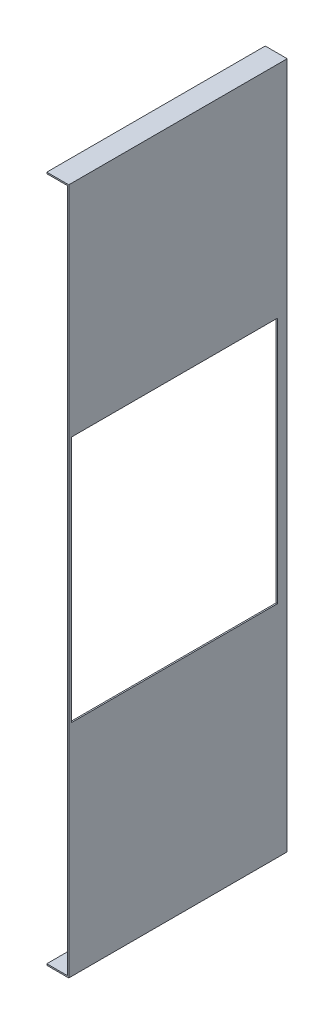
SolidWorks part; units mm, degrees
material "1023 Carbon Steel Sheet (SS)"
ref_plane "Front Plane" through (0, 0, 0) normal (0, 0, 1) x (1, 0, 0)
ref_plane "Top Plane" through (0, 0, 0) normal (0, 1, 0) x (1, 0, 0)
ref_plane "Right Plane" through (0, 0, 0) normal (1, 0, 0) x (0, 0, -1)
sketch "Sketch1" plane through (0, 0, 0) normal (0, 0, 1) x (1, 0, 0)
  line L0 (-0.5, -249) -> (-15.5, -249)
  line L2 (-0.5, 249) -> (-0.5, -249)
  line L4 (0.5, 249) -> (0.5, -249)
  line L5 (-0.5, 249) -> (0.5, -249) construction
  line L6 (-0.5, -249) -> (0.5, 249) construction
  line L7 (0.5, -250) -> (-15.5, -250)
  line L8 (0.5, -249) -> (0.5, -250)
  line L9 (-15.5, -249) -> (-15.5, -250)
  line L10 (0, 0) -> (-2.3545, 0) construction
  line L11 (0.5, 249) -> (0.5, 250)
  line L12 (-15.5, 249) -> (-15.5, 250)
  line L13 (0.5, 250) -> (-15.5, 250)
  line L14 (-0.5, 249) -> (-15.5, 249)
  point P0 (0, 0)
  dimension "D1" = 498
  dimension "D2" = 1
  dimension "D3" = 15
  dimension "D4" = 16
extrude "Boss-Extrude1" add sketch "Sketch1" along normal blind 159
sketch "Sketch3" plane through (0.5, 0, 0) normal (1, 0, 0) x (0, 0, -1)
  line L0 (-159, -250) -> (-159, 250) construction
  line L1 (-157, 90) -> (-7, 90)
  line L2 (-157, 90) -> (-157, -90)
  line L3 (-157, -90) -> (-7, -90)
  line L4 (-7, 90) -> (-7, -90)
  line L5 (-157, 90) -> (-7, -90) construction
  line L6 (-157, -90) -> (-7, 90) construction
  line L7 (-159, -250) -> (0, -250) construction
  line L9 (-159, 250) -> (0, 250) construction
  point P0 (-82, 0)
  dimension "D1" = 2
  dimension "D2" = 180
  dimension "D3" = 150
  dimension "D4" = 250
  dimension "D5" = 250
extrude "Cut-Extrude1" cut sketch "Sketch3" against normal through all
